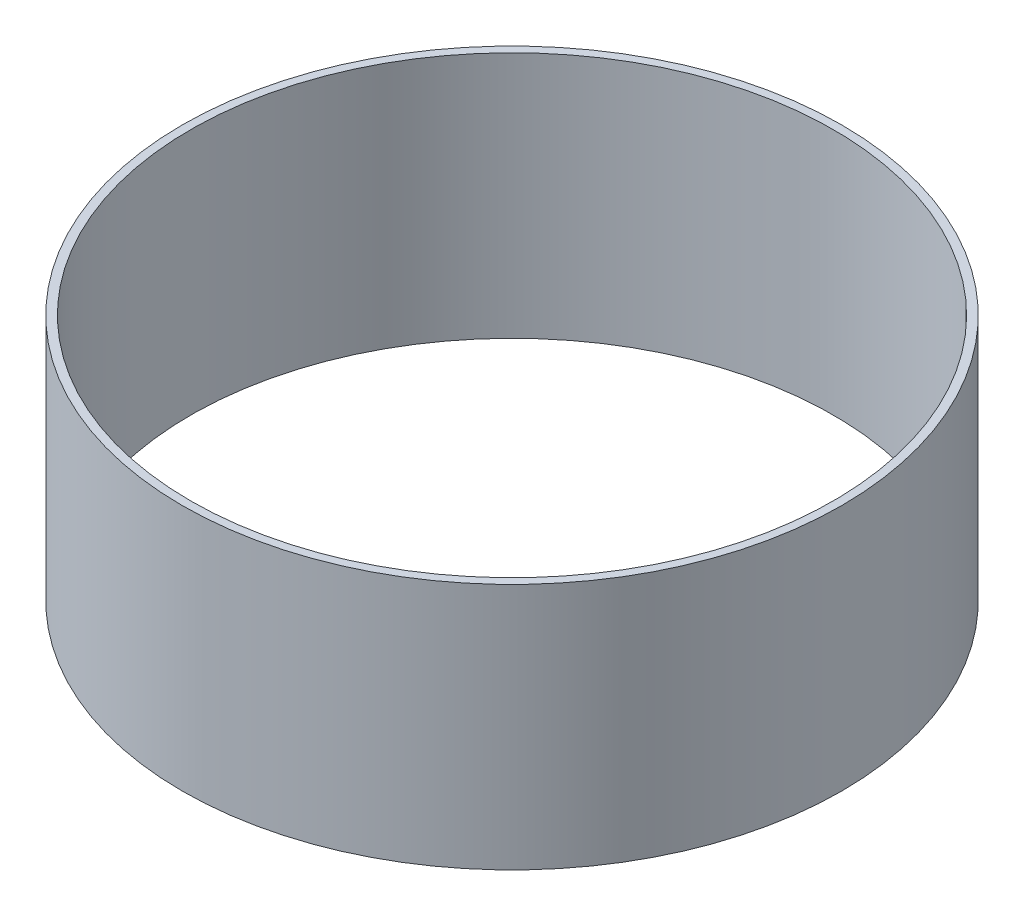
SolidWorks part; units mm, degrees
material "Polyurethane Foam Flexible"
ref_plane "Front Plane" through (0, 0, 0) normal (0, 0, 1) x (1, 0, 0)
ref_plane "Top Plane" through (0, 0, 0) normal (0, 1, 0) x (1, 0, 0)
ref_plane "Right Plane" through (0, 0, 0) normal (1, 0, 0) x (0, 0, -1)
sketch "Sketch1" plane through (0, 0, 0) normal (0, 1, 0) x (1, 0, 0)
  circle A0 centre (0, 0) radius 400
  circle A1 centre (0, 0) radius 390
  dimension "D1" = 800
  dimension "D2" = 780
extrude "Boss-Extrude1" add sketch "Sketch1" along normal blind 300
